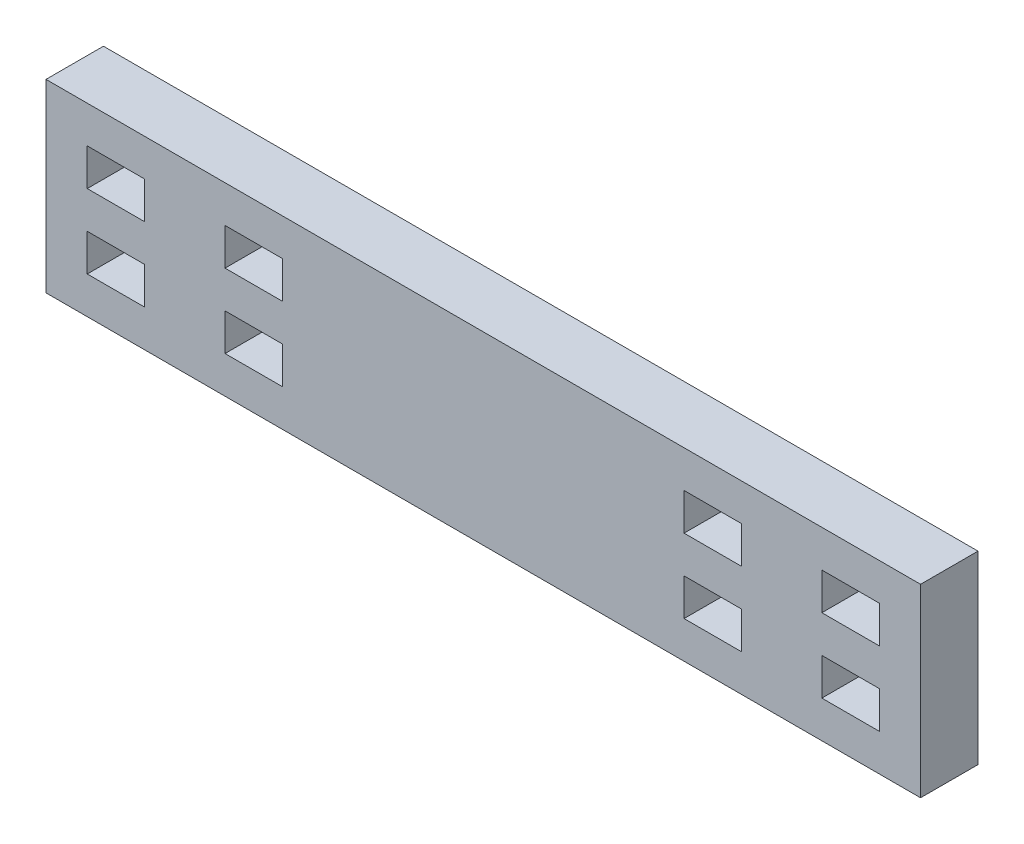
SolidWorks part; units mm, degrees
ref_plane "Front Plane" through (0, 0, 0) normal (0, 0, 1) x (1, 0, 0)
ref_plane "Top Plane" through (0, 0, 0) normal (0, 1, 0) x (1, 0, 0)
ref_plane "Right Plane" through (0, 0, 0) normal (1, 0, 0) x (0, 0, -1)
sketch "Sketch1" plane through (0, 0, 0) normal (0, 0, 1) x (1, 0, 0)
  line L1 (0, 0) -> (78.4, 0)
  line L2 (0, 0) -> (0, 16.577)
  line L3 (0, 16.577) -> (78.4, 16.577)
  line L4 (78.4, 0) -> (78.4, 16.577)
  dimension "D1" = 16.577
  dimension "D2" = 78.4
extrude "Boss-Extrude1" add sketch "Sketch1" along normal blind 5.15
sketch "Sketch2" plane through (0, 0, 5.15) normal (0, 0, 1) x (1, 0, 0)
  line L0 (39.2, 16.577) -> (39.2, -17.0511) construction
  line L1 (78.4, 16.577) -> (0, 16.577) construction
  line L2 (6.8477, 16.577) -> (6.8477, 13.2616) construction
  line L3 (3.697, 13.2616) -> (8.847, 13.2616)
  line L4 (3.697, 13.2616) -> (3.697, 9.9462)
  line L5 (3.697, 9.9462) -> (8.847, 9.9462)
  line L6 (8.847, 13.2616) -> (8.847, 9.9462)
  line L7 (3.697, 6.6308) -> (8.847, 6.6308)
  line L8 (3.697, 6.6308) -> (3.697, 3.3154)
  line L9 (3.697, 3.3154) -> (8.847, 3.3154)
  line L10 (8.847, 6.6308) -> (8.847, 3.3154)
  line L11 (16.05, 13.2616) -> (21.2, 13.2616)
  line L12 (16.05, 13.2616) -> (16.05, 9.9462)
  line L13 (16.05, 9.9462) -> (21.2, 9.9462)
  line L14 (21.2, 13.2616) -> (21.2, 9.9462)
  line L15 (16.05, 6.6308) -> (21.2, 6.6308)
  line L16 (16.05, 6.6308) -> (16.05, 3.3154)
  line L17 (16.05, 3.3154) -> (21.2, 3.3154)
  line L18 (21.2, 6.6308) -> (21.2, 3.3154)
  line L19 (6.8477, 9.9462) -> (6.8477, 6.6308) construction
  line L20 (6.272, 3.3154) -> (6.272, 0) construction
  line L21 (2.8325, 0) -> (-2.8325, 0) construction
  line L22 (57.2, 6.6308) -> (57.2, 3.3154)
  line L23 (62.35, 3.3154) -> (57.2, 3.3154)
  line L24 (62.35, 6.6308) -> (62.35, 3.3154)
  line L25 (62.35, 6.6308) -> (57.2, 6.6308)
  line L26 (57.2, 13.2616) -> (57.2, 9.9462)
  line L27 (62.35, 9.9462) -> (57.2, 9.9462)
  line L28 (62.35, 13.2616) -> (62.35, 9.9462)
  line L29 (62.35, 13.2616) -> (57.2, 13.2616)
  line L30 (69.553, 6.6308) -> (69.553, 3.3154)
  line L31 (74.703, 3.3154) -> (69.553, 3.3154)
  line L32 (74.703, 6.6308) -> (74.703, 3.3154)
  line L33 (74.703, 6.6308) -> (69.553, 6.6308)
  line L34 (69.553, 13.2616) -> (69.553, 9.9462)
  line L35 (74.703, 9.9462) -> (69.553, 9.9462)
  line L36 (74.703, 13.2616) -> (74.703, 9.9462)
  line L37 (74.703, 13.2616) -> (69.553, 13.2616)
  dimension "D1" = 5.15
  dimension "D2" = 5.15
  dimension "D3" = 18
extrude "Cut-Extrude1" cut sketch "Sketch2" against normal through all
